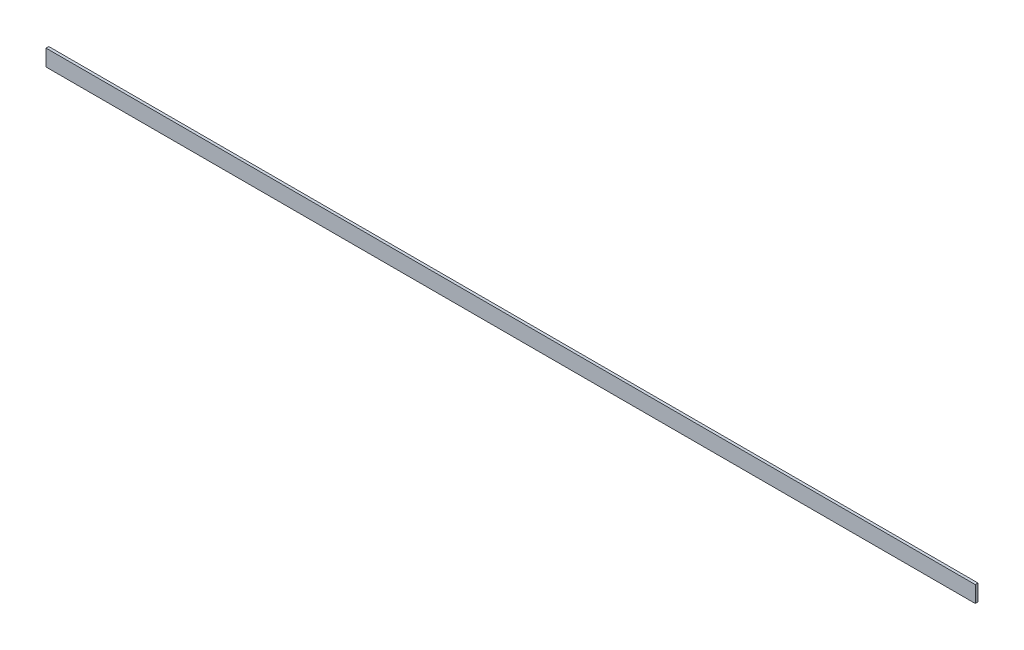
SolidWorks part; units mm, degrees
ref_plane "Спереди" through (0, 0, 0) normal (0, 0, 1) x (1, 0, 0)
ref_plane "Сверху" through (0, 0, 0) normal (0, 1, 0) x (1, 0, 0)
ref_plane "Справа" through (0, 0, 0) normal (1, 0, 0) x (0, 0, -1)
sketch "Эскиз1" plane through (0, 0, 0) normal (1, 0, 0) x (0, 0, -1)
  line L1 (0, 0) -> (5, 0)
  line L2 (0, 0) -> (0, 30)
  line L3 (0, 30) -> (5, 30)
  line L4 (5, 0) -> (5, 30)
extrude "Бобышка-Вытянуть1" add sketch "Эскиз1" along normal blind 1700
